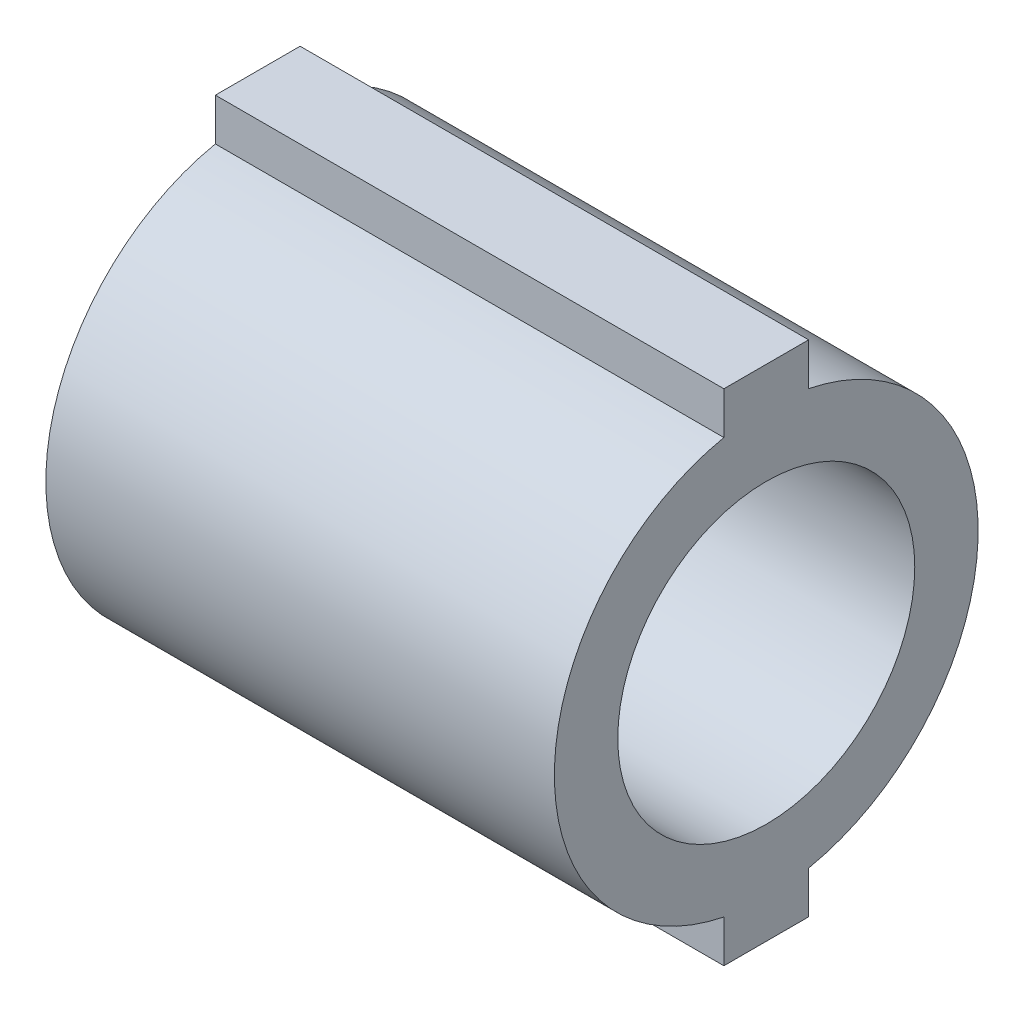
SolidWorks part; units mm, degrees
ref_plane "Front Plane" through (0, 0, 0) normal (0, 0, 1) x (1, 0, 0)
ref_plane "Top Plane" through (0, 0, 0) normal (0, 1, 0) x (1, 0, 0)
ref_plane "Right Plane" through (0, 0, 0) normal (1, 0, 0) x (0, 0, -1)
sketch "Sketch1" plane through (0, 0, 0) normal (1, 0, 0) x (0, 0, -1)
  circle A0 centre (0, 0) radius 7.9375
  dimension "D1" = 15.875
extrude "Boss-Extrude1" add sketch "Sketch1" along normal blind 19.05
sketch "Sketch2" plane through (0, 0, 0) normal (-1, 0, 0) x (0, 0, 1)
  line L0 (0, 0) -> (-15.2868, 0) construction
  line L1 (-1.5875, 5.913) -> (1.5875, 5.913)
  line L2 (-1.5875, 5.913) -> (-1.5875, 9.3599)
  line L3 (-1.5875, 9.3599) -> (1.5875, 9.3599)
  line L4 (1.5875, 5.913) -> (1.5875, 9.3599)
  line L5 (-1.5875, -9.3599) -> (1.5875, -9.3599)
  line L6 (1.5875, -5.913) -> (1.5875, -9.3599)
  line L7 (-1.5875, -5.913) -> (1.5875, -5.913)
  line L8 (-1.5875, -5.913) -> (-1.5875, -9.3599)
  point P12 (0, 5.913)
  dimension "D1" = 3.175
  dimension "D2" = 18.7198
extrude "Boss-Extrude2" add sketch "Sketch2" against normal up to surface (19.05 mm away) up to face at (19.05, 0, -7.9375)
sketch "Sketch3" plane through (0, 0, 0) normal (-1, 0, 0) x (0, 0, 1)
  circle A0 centre (0, 0) radius 5.5626
  dimension "D1" = 11.1252
extrude "Cut-Extrude1" cut sketch "Sketch3" against normal up to surface (19.05 mm away) up to face at (19.05, 0, 0)
